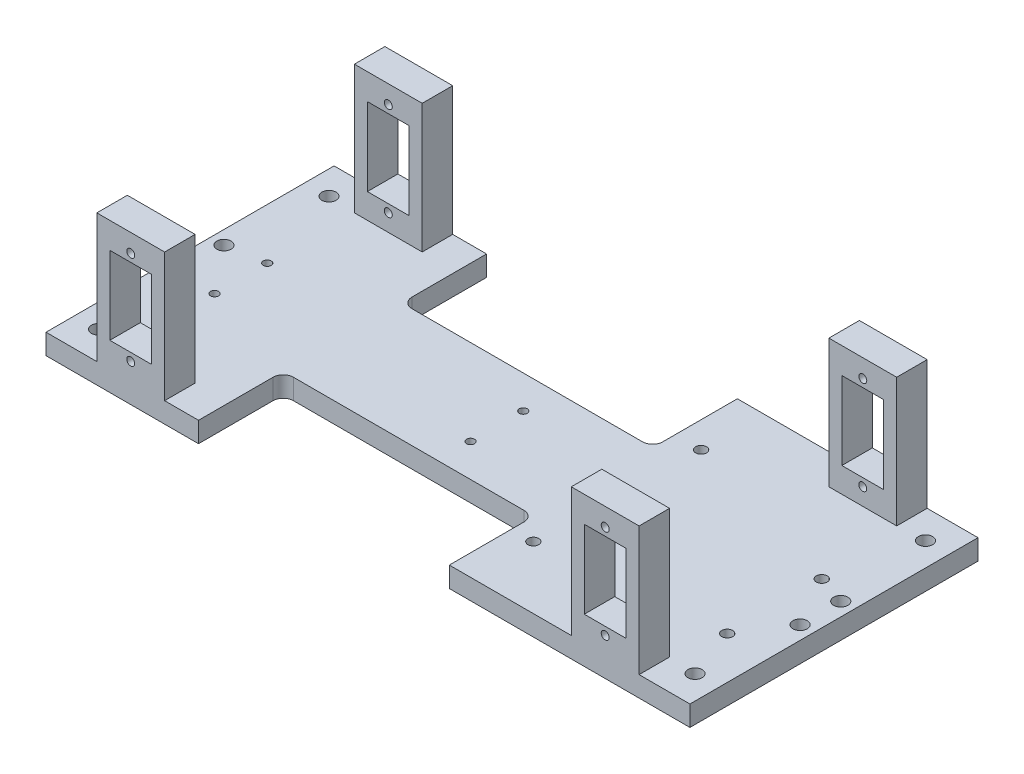
SolidWorks part; units mm, degrees
ref_plane "Front Plane" through (0, 0, 0) normal (0, 0, 1) x (1, 0, 0)
ref_plane "Top Plane" through (0, 0, 0) normal (0, 1, 0) x (1, 0, 0)
ref_plane "Right Plane" through (0, 0, 0) normal (1, 0, 0) x (0, 0, -1)
sketch "Sketch1" plane through (0, 0, 0) normal (0, 1, 0) x (1, 0, 0)
  line L1 (-95, 42.5) -> (95, 42.5)
  line L2 (-95, 42.5) -> (-95, -42.5)
  line L3 (-95, -42.5) -> (95, -42.5)
  line L4 (95, 42.5) -> (95, -42.5)
  line L5 (-95, 42.5) -> (95, -42.5) construction
  line L6 (-95, -42.5) -> (95, 42.5) construction
  point P0 (0, 0)
  dimension "D1" = 85
  dimension "D2" = 190
extrude "Boss-Extrude1" add sketch "Sketch1" along normal blind 6
sketch "Sketch2" plane through (0, 6, 0) normal (0, 1, 0) x (1, 0, 0)
  line L0 (-95, -42.5) -> (95, -42.5) construction
  line L1 (60, -42.5) -> (80, -42.5)
  line L2 (60, -42.5) -> (60, -33.5)
  line L3 (60, -33.5) -> (80, -33.5)
  line L4 (80, -42.5) -> (80, -33.5)
  line L5 (95, -42.5) -> (95, 42.5) construction
  dimension "D1" = 20
  dimension "D2" = 9
  dimension "D3" = 15
extrude "Boss-Extrude2" add sketch "Sketch2" along normal blind 38
sketch "Sketch3" plane through (0, 0, 42.5) normal (0, 0, 1) x (1, 0, 0)
  line L0 (80, 44) -> (80, 6) construction
  line L1 (63.825, 36.35) -> (76.175, 36.35)
  line L2 (63.825, 36.35) -> (63.825, 13.35)
  line L3 (63.825, 13.35) -> (76.175, 13.35)
  line L4 (76.175, 36.35) -> (76.175, 13.35)
  line L5 (60, 44) -> (80, 44) construction
  line L6 (50.721, 24.85) -> (81.9936, 24.85) construction
  circle A0 centre (70, 38.67) radius 1.175
  circle A1 centre (70, 11.03) radius 1.175
  dimension "D6" = 2.35
  dimension "D1" = 12.35
  dimension "D2" = 3.825
  dimension "D3" = 23
  dimension "D4" = 7.65
  dimension "D5" = 10
  dimension "D7" = 2.32
  dimension "D8" = 11.5
extrude "Cut-Extrude1" cut sketch "Sketch3" against normal blind 30
sketch "Sketch5" plane through (0, 6, 0) normal (0, 1, 0) x (1, 0, 0)
  line L0 (112.6778, 0) -> (-101.3487, 0) construction
sketch "Sketch7" plane through (0, 0, 0) normal (0, -1, 0) x (-1, 0, 0)
  line L0 (55.5412, 0) -> (-53.7929, 0) construction
  line L1 (-112.6778, 0) -> (101.3487, 0) construction
ref_plane "Plane1" through (0, 0, 0) normal (0, 0, 1) x (1, 0, 0)
mirror "Mirror1" about plane through (0, 0, 0) normal (0, 0, 1) of "Cut-Extrude1", "Boss-Extrude2"
sketch "Sketch9" plane through (0, 0, 42.5) normal (0, 0, 1) x (1, 0, 0)
  line L0 (0, 0) -> (0, 81.3526) construction
  line L1 (-95, 0) -> (95, 0) construction
ref_plane "Plane2" through (0, 0, 0) normal (-1, 0, 0) x (0, 0, 1)
mirror "Mirror2" about plane through (0, 0, 0) normal (-1, 0, 0) of "Mirror1", "Cut-Extrude1", "Boss-Extrude2"
sketch "Sketch10" plane through (0, 6, 0) normal (0, 1, 0) x (1, 0, 0)
  line L1 (112.6778, 0) -> (-101.3487, 0) construction
  line L2 (95, -42.5) -> (95, 42.5) construction
  circle A0 centre (31.7, 24.1) radius 1.6
  circle A2 centre (82.5, 8.9) radius 1.6
  circle A3 centre (82.5, -19) radius 1.6
  circle A5 centre (30.4, -24.1) radius 1.6
  dimension "D1" = 3.2
  dimension "D3" = 1.3
  dimension "D10" = 3.2
  dimension "D11" = 3.2
  dimension "D12" = 3.2
  dimension "D2" = 27.9
  dimension "D4" = 48.2
  dimension "D5" = 5.1
  dimension "D6" = 15.2
  dimension "D7" = 50.8
  dimension "D8" = 8.9
  dimension "D9" = 12.5
extrude "Cut-Extrude2" cut sketch "Sketch10" against normal blind 6
sketch "Sketch11" plane through (0, 6, 0) normal (0, 1, 0) x (1, 0, 0)
  line L1 (95, 42.5) -> (80, 42.5) construction
  line L2 (95, -42.5) -> (95, 42.5) construction
  line L3 (122.8018, 0) -> (-36.7177, 0) construction
  line L4 (0, -64.9142) -> (0, 104.2009) construction
  circle A0 centre (88, 34) radius 2.1
  circle A1 centre (88, -34) radius 2.1
  circle A2 centre (-88, 34) radius 2.1
  circle A3 centre (-88, -34) radius 2.1
  dimension "D1" = 4.2
  dimension "D2" = 8.5
  dimension "D3" = 7
extrude "Cut-Extrude3" cut sketch "Sketch11" against normal blind 10
sketch "Sketch13" plane through (0, 6, 0) normal (0, 1, 0) x (1, 0, 0)
  line L0 (-95, 42.5) -> (-95, -42.5) construction
  line L1 (0, 0) -> (-111.7259, 0) construction
  circle A0 centre (-4.45, 7.775) radius 1.175
  circle A1 centre (-4.45, -7.775) radius 1.175
  circle A2 centre (-80, 7.775) radius 1.175
  circle A3 centre (-80, -7.775) radius 1.175
  dimension "D6" = 2.35
  dimension "D7" = 2.35
  dimension "D8" = 2.35
  dimension "D9" = 2.35
  dimension "D1" = 15.55
  dimension "D2" = 15.55
  dimension "D3" = 0
  dimension "D4" = 15
  dimension "D5" = 0
  dimension "D10" = 75.55
  dimension "D11" = 0
  dimension "D12" = 7.775
sketch "Sketch15" plane through (0, 6, 0) normal (0, 1, 0) x (1, 0, 0)
  line L0 (60, 42.5) -> (-60, 42.5) construction
  line L1 (-50, 42.5) -> (24, 42.5)
  line L2 (-50, 42.5) -> (-50, 17.5)
  line L3 (-50, 17.5) -> (24, 17.5)
  line L4 (24, 42.5) -> (24, 17.5)
  line L5 (-60, 33.5) -> (-60, 42.5) construction
  line L6 (0, 0) -> (-82.7928, 0) construction
  line L7 (-50, -17.5) -> (24, -17.5)
  line L8 (24, -42.5) -> (24, -17.5)
  line L9 (-50, -42.5) -> (24, -42.5)
  line L10 (-50, -42.5) -> (-50, -17.5)
  dimension "D1" = 74
  dimension "D2" = 10
  dimension "D3" = 25
extrude "Cut-Extrude5" cut sketch "Sketch15" against normal blind 10
fillet "Fillet3" radius 3 4 edges at (24, 3, 17.5) (-50, 3, 17.5) (-50, 3, -17.5) (24, 3, -17.5)
sketch "Sketch16" plane through (0, 6, 0) normal (0, 1, 0) x (1, 0, 0)
  line L0 (0, -72.4115) -> (0, 67.2832) construction
  line L1 (95, -42.5) -> (95, 42.5) construction
  line L2 (80, -42.5) -> (95, -42.5) construction
  circle A0 centre (91, 6) radius 2.1
  circle A1 centre (91, -6) radius 2.1
  circle A2 centre (-91, 6) radius 2.1
  circle A3 centre (-91, -6) radius 2.1
  dimension "D1" = 4.2
  dimension "D2" = 4.2
  dimension "D3" = 12
  dimension "D4" = 4
  dimension "D5" = 4
  dimension "D6" = 36.5
extrude "Cut-Extrude6" cut sketch "Sketch16" against normal blind 10
extrude "Cut-Extrude7" cut sketch "Sketch13" against normal blind 10
